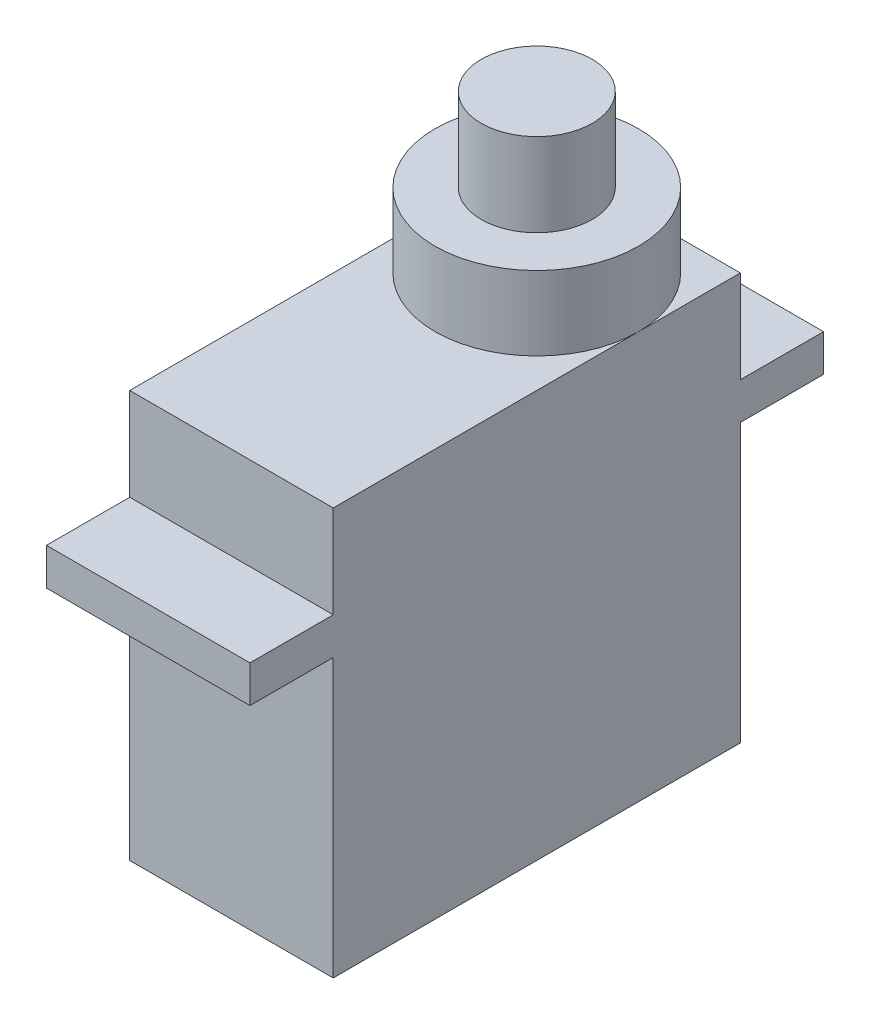
SolidWorks part; units mm, degrees
ref_plane "Front Plane" through (0, 0, 0) normal (0, 0, 1) x (1, 0, 0)
ref_plane "Top Plane" through (0, 0, 0) normal (0, 1, 0) x (1, 0, 0)
ref_plane "Right Plane" through (0, 0, 0) normal (1, 0, 0) x (0, 0, -1)
sketch "Sketch2" plane through (0, 0, 0) normal (0, 1, 0) x (1, 0, 0)
  line L1 (-5.5, -11) -> (5.5, -11)
  line L2 (-5.5, -11) -> (-5.5, 11)
  line L3 (-5.5, 11) -> (5.5, 11)
  line L4 (5.5, -11) -> (5.5, 11)
  line L5 (-5.5, -11) -> (5.5, 11) construction
  line L6 (-5.5, 11) -> (5.5, -11) construction
  point P0 (0, 0)
  dimension "D1" = 22
  dimension "D2" = 11
extrude "Boss-Extrude1" add sketch "Sketch2" along normal blind 22
ref_plane "Plane1" through (0, 15, 0) normal (0, 1, 0) x (1, 0, 0)
sketch "Sketch3" plane through (0, 15, 0) normal (0, 1, 0) x (1, 0, 0)
  line L0 (0, 11) -> (0, 15.5) construction
  line L1 (5.5, 11) -> (-5.5, 11) construction
  line L2 (-5.5, 0) -> (5.5, 0) construction
  line L3 (-5.5, 11) -> (-5.5, -11) construction
  line L4 (5.5, -11) -> (5.5, 11) construction
  line L5 (-5.5, 11) -> (-5.5, 15.5)
  line L6 (-5.5, 15.5) -> (5.5, 15.5)
  line L7 (5.5, 15.5) -> (5.5, 11)
  line L8 (-5.5, 11) -> (5.5, 11)
  line L9 (-5.5, -11) -> (-5.5, -15.5)
  line L10 (-5.5, -11) -> (5.5, -11)
  line L11 (5.5, -15.5) -> (5.5, -11)
  line L12 (-5.5, -15.5) -> (5.5, -15.5)
  dimension "D1" = 4.5
extrude "Boss-Extrude2" add sketch "Sketch3" along normal blind 2
sketch "Sketch4" plane through (0, 22, 0) normal (0, 1, 0) x (1, 0, 0)
  line L0 (0, 15.5) -> (0, -15.5) construction
  line L1 (5.5, 15.5) -> (-5.5, 15.5) construction
  line L2 (-5.5, -15.5) -> (5.5, -15.5) construction
  line L3 (-5.5, 11) -> (5.5, 11) construction
  line L4 (0, 11) -> (0, 5.5) construction
  circle A0 centre (0, 5.5) radius 5.5
  dimension "D1" = 5.5
  dimension "D2" = 11
extrude "Boss-Extrude3" add sketch "Sketch4" along normal blind 4
sketch "Sketch5" plane through (0, 26, 0) normal (0, 1, 0) x (1, 0, 0)
  line L0 (0, 11) -> (0, 0) construction
  line L1 (-5.5, 11) -> (5.5, 11) construction
  circle A0 centre (0, 5.5) radius 3
  dimension "D1" = 6
extrude "Boss-Extrude4" add sketch "Sketch5" along normal blind 4.5
